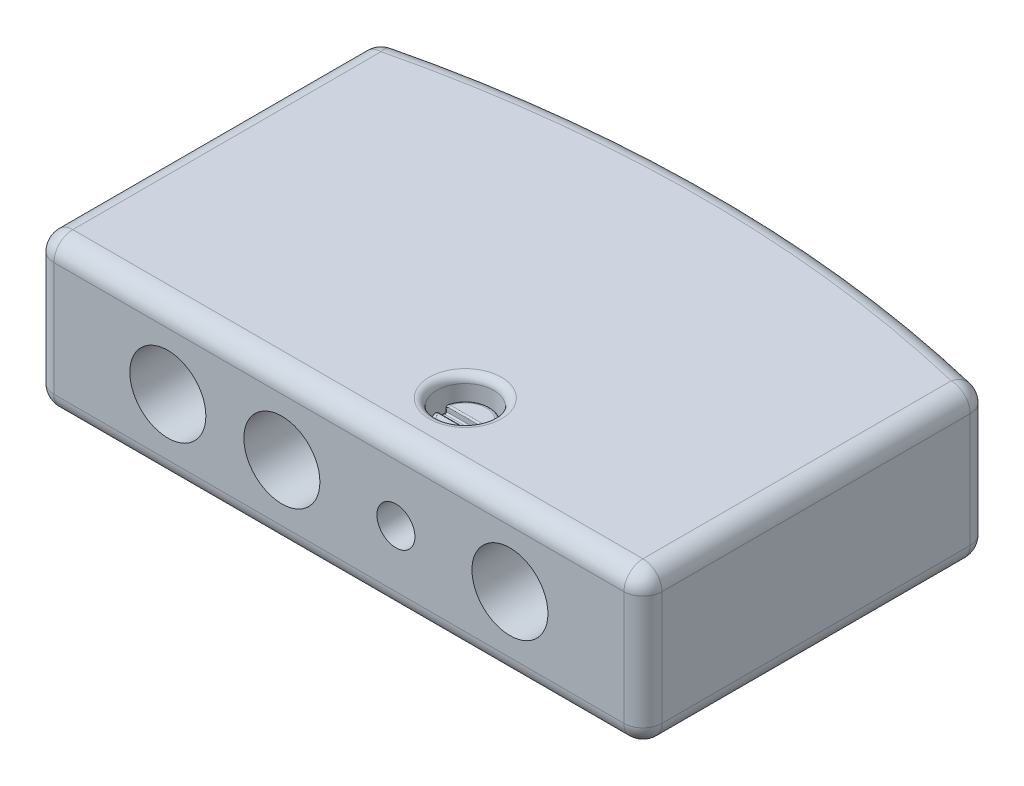
SolidWorks part; units mm, degrees
ref_plane "Front Plane" through (0, 0, 0) normal (0, 0, 1) x (1, 0, 0)
ref_plane "Top Plane" through (0, 0, 0) normal (0, 1, 0) x (1, 0, 0)
ref_plane "Right Plane" through (0, 0, 0) normal (1, 0, 0) x (0, 0, -1)
sketch "Sketch1" plane through (0, 0, 0) normal (0, 0, 1) x (1, 0, 0)
  line L0 (0, -55) -> (0, 55) construction
  line L1 (-4, 1) -> (4, 1)
  line L2 (-4, 1) -> (-4, -1)
  line L3 (-4, -1) -> (4, -1)
  line L4 (4, 1) -> (4, -1)
  line L5 (55, 0) -> (-55, 0) construction
  dimension "D1" = 8
  dimension "D2" = 4
  dimension "D3" = 2
  dimension "D4" = 1
extrude "Boss-Extrude1" add sketch "Sketch1" along normal blind 5
sketch "Sketch2" plane through (0, 1, 0) normal (0, 1, 0) x (1, 0, 0)
  line L0 (-4, -5) -> (-4, 0) construction
  line L1 (4, -5) -> (4, 0) construction
  line L2 (-1.1, 0) -> (1.1, 0) construction
  line L3 (-4, -0.5) -> (-4.5994, 0)
  line L4 (-4.5994, 0) -> (-3.0751, 0.9055)
  line L5 (-3.0751, 0.9055) -> (5.0664, 0.7028)
  line L6 (5.0664, 0.7028) -> (4, -0.5)
  line L7 (4, -0.5) -> (4.009, -0.4779)
  arc A0 (-4, -0.5) -> (4, -0.5) centre (0, -16.25) cw
  line M1 (4, 0) -> (-4, 0)
  line M2 (-4, 0) -> (-4, -5)
  line M4 (4, -5) -> (4, 0)
  dimension "D1" = 0.5
  dimension "D2" = 0.5
extrude "Cut-Extrude1" cut sketch "Sketch2" against normal blind 5 contours A0 M2 M1 | A0 M1 M4
sketch "Sketch3" plane through (0, 0, 5) normal (0, 0, 1) x (1, 0, 0)
  line L0 (2.75, 0) -> (-2.75, 0) construction
  line L1 (0, -1.1) -> (0, 1.1) construction
  circle A0 centre (-2.25, 0) radius 0.5
  circle A1 centre (-0.75, 0) radius 0.5
  circle A2 centre (0.75, 0) radius 0.25
  circle A3 centre (2.25, 0) radius 0.5
  dimension "D2" = 1
  dimension "D4" = 0.5
  dimension "D6" = 1
  dimension "D8" = 1
  dimension "D1" = 0.75
  dimension "D3" = 0.75
  dimension "D5" = 1.5
  dimension "D7" = 1.5
extrude "Cut-Extrude2" cut sketch "Sketch3" against normal blind 2
fillet "Fillet1" radius 0.25 12 edges at (-4, 0, 5) (-4, 0, 0.5) (-4, -1, 2.75) (0, -1, 5) (4, -1, 2.75) (0, -1, 0) (0, 1, 5) (-4, 1, 2.75) (0, 1, 0) (4, 1, 2.75) (4, 0, 5) (4, 0, 0.5)
sketch "Sketch4" plane through (0, 1, 0) normal (0, 1, 0) x (1, 0, 0)
  circle A0 centre (0.75, -4.087) radius 0.375
  dimension "D1" = 0.75
extrude "Cut-Extrude3" cut sketch "Sketch4" against normal blind 0.5
sketch "Sketch5" plane through (0, 0.5, 0) normal (0, 1, 0) x (1, 0, 0)
  circle A0 centre (0.75, -4.087) radius 0.325
  dimension "D1" = 0.65
extrude "Boss-Extrude2" add sketch "Sketch5" along normal blind 0.25
sketch "Sketch6" plane through (0, 0.75, 0) normal (0, 1, 0) x (-1, 0, 0)
  line L1 (-0.4011, 4.0362) -> (-1.0939, 4.0362)
  line L2 (-0.4011, 4.0362) -> (-0.4011, 4.17)
  line L3 (-0.4011, 4.17) -> (-1.0939, 4.17)
  line L4 (-1.0939, 4.0362) -> (-1.0939, 4.17)
  dimension "D1" = 0.6929
extrude "Cut-Extrude4" cut sketch "Sketch6" against normal blind 0.1
fillet "Fillet2" radius 0.1 1 edges at (0.75, 1, 4.462)
fillet "Fillet3" radius 0.05 2 edges at (0.75, 0.75, 4.412) (0.75, 0.75, 3.762)
mirror "Mirror3" about plane through (0, 0, 0) normal (0, 1, 0) of "Fillet3", "Cut-Extrude4", "Boss-Extrude2", "Fillet2", "Cut-Extrude3"
fillet "Fillet4" radius 0.02 14 edges at (0.75, 0.75, 4.17) (0.75, 0.75, 4.0362) (1.0459, 0.7382, 4.17) (0.4464, 0.7304, 4.17) (0.4476, 0.7388, 4.0362) (1.0601, 0.7309, 4.0362) (1.0642, 0.675, 4.17) (0.4358, 0.675, 4.17) (0.429, 0.675, 4.0362) (1.071, 0.675, 4.0362) (0.75, 0.65, 4.17) (1.0746, 0.65, 4.1034) (0.4254, 0.65, 4.1034) (0.75, 0.65, 4.0362)
fillet "Fillet5" radius 0.02 14 edges at (0.75, -0.75, 4.0362) (0.75, -0.75, 4.17) (1.0601, -0.7309, 4.0362) (0.4476, -0.7388, 4.0362) (0.4464, -0.7304, 4.17) (1.0459, -0.7382, 4.17) (1.071, -0.675, 4.0362) (0.429, -0.675, 4.0362) (0.4358, -0.675, 4.17) (1.0642, -0.675, 4.17) (0.75, -0.65, 4.0362) (1.0746, -0.65, 4.1034) (0.4254, -0.65, 4.1034) (0.75, -0.65, 4.17)
